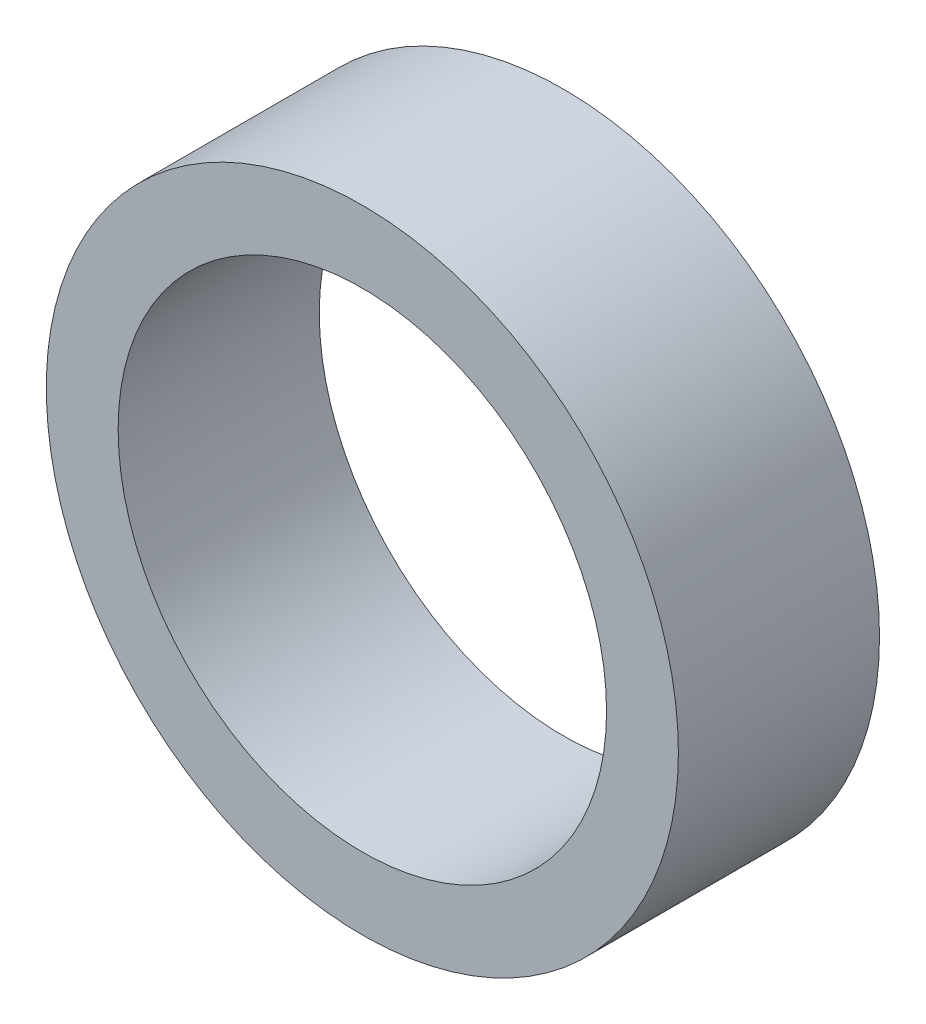
SolidWorks part; units mm, degrees
ref_plane "Front Plane" through (0, 0, 0) normal (0, 0, 1) x (1, 0, 0)
ref_plane "Top Plane" through (0, 0, 0) normal (0, 1, 0) x (1, 0, 0)
ref_plane "Right Plane" through (0, 0, 0) normal (1, 0, 0) x (0, 0, -1)
sketch "Sketch1" plane through (0, 0, 0) normal (0, 0, 1) x (1, 0, 0)
  circle A0 centre (0, 0) radius 11
  circle A1 centre (0, 0) radius 8.5
  dimension "D1" = 17
  dimension "D2" = 22
extrude "Boss-Extrude1" add sketch "Sketch1" along normal blind 7
